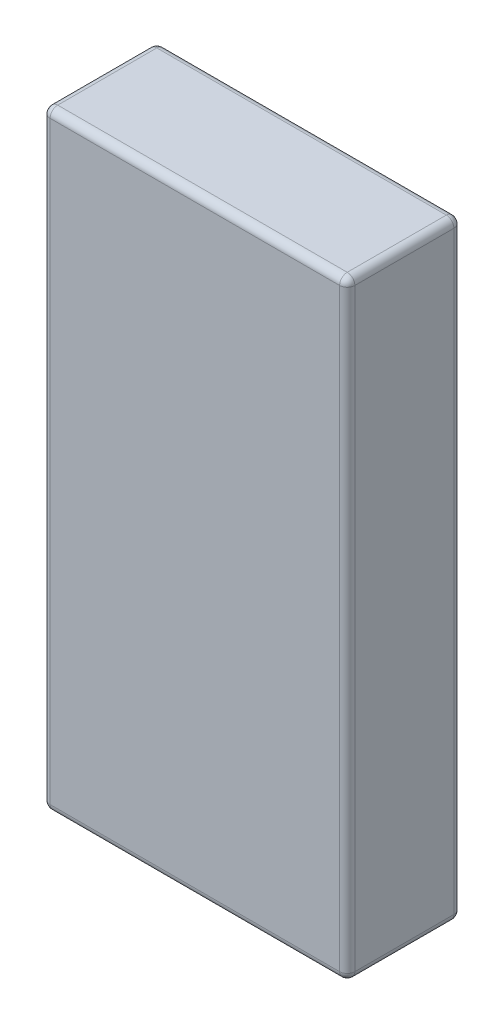
SolidWorks part; units mm, degrees
material "Neodymium (N-35)"
ref_plane "Front Plane" through (0, 0, 0) normal (0, 0, 1) x (1, 0, 0)
ref_plane "Top Plane" through (0, 0, 0) normal (0, 1, 0) x (1, 0, 0)
ref_plane "Right Plane" through (0, 0, 0) normal (1, 0, 0) x (0, 0, -1)
sketch "Sketch1" plane through (0, 0, 0) normal (0, 0, 1) x (1, 0, 0)
  line L1 (-2, -4) -> (2, -4)
  line L2 (-2, -4) -> (-2, 4)
  line L3 (-2, 4) -> (2, 4)
  line L4 (2, -4) -> (2, 4)
  line L5 (-2, -4) -> (2, 4) construction
  line L6 (-2, 4) -> (2, -4) construction
  point P0 (0, 0)
  dimension "D1" = 4
  dimension "D2" = 8
extrude "Boss-Extrude1" add sketch "Sketch1" along normal blind 1.5
fillet "Fillet1" radius 0.1 12 edges at (-2, 0, 1.5) (2, 0, 1.5) (-2, -4, 0.75) (0, -4, 1.5) (0, 4, 1.5) (-2, 4, 0.75) (2, -4, 0.75) (2, 4, 0.75) (0, 4, 0) (-2, 0, 0) (0, -4, 0) (2, 0, 0)
